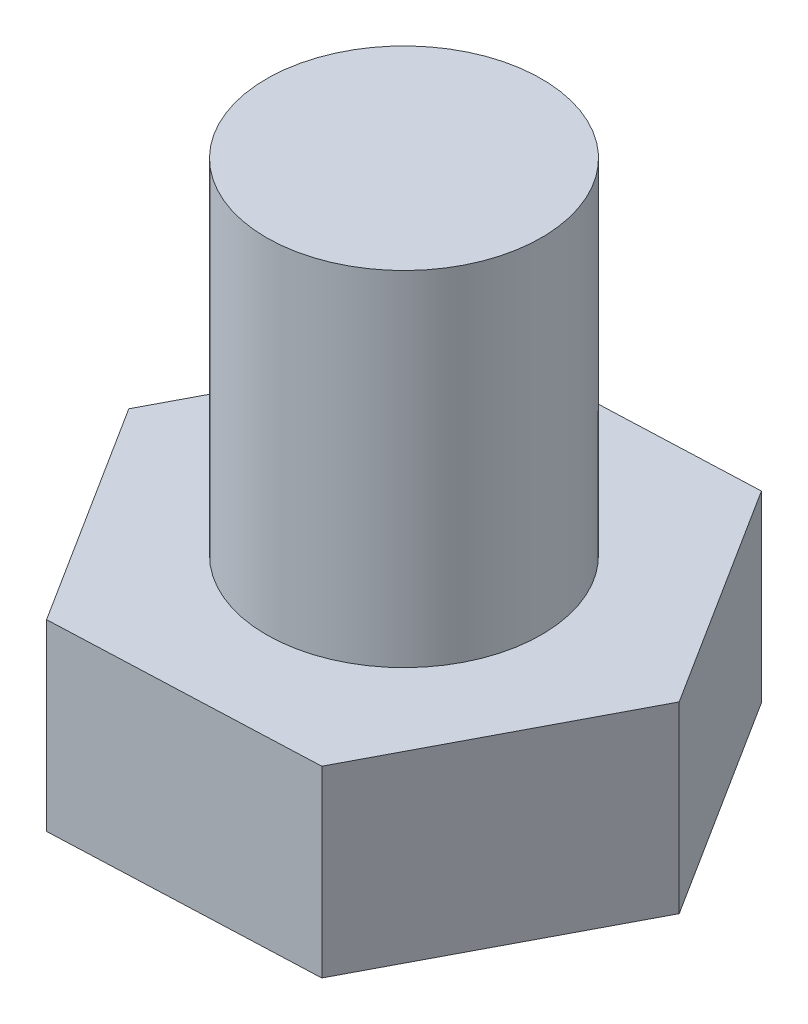
SolidWorks part; units mm, degrees
ref_plane "Front" through (0, 0, 0) normal (0, 0, 1) x (1, 0, 0)
ref_plane "Top" through (0, 0, 0) normal (0, 1, 0) x (1, 0, 0)
ref_plane "Right" through (0, 0, 0) normal (1, 0, 0) x (0, 0, -1)
sketch "Croquis1" plane through (0, 0, 0) normal (0, 1, 0) x (1, 0, 0)
  line L1 (6.1723, -9.7589) -> (11.5376, 0.4659)
  line L2 (11.5376, 0.4659) -> (5.3653, 10.2248)
  line L3 (5.3653, 10.2248) -> (-6.1723, 9.7589)
  line L4 (-6.1723, 9.7589) -> (-11.5376, -0.4659)
  line L5 (-11.5376, -0.4659) -> (-5.3653, -10.2248)
  line L6 (-5.3653, -10.2248) -> (6.1723, -9.7589)
  circle A0 centre (0, 0) radius 10 construction
  dimension "D1" = 20
extrude "Saliente-Extruir1" add sketch "Croquis1" along normal blind 8 contours L3 L4 L5 L6 L1 L2
sketch "Croquis2" plane through (0, 8, 0) normal (0, 1, 0) x (1, 0, 0)
  circle A0 centre (0, 0) radius 6
  dimension "D1" = 12
extrude "Saliente-Extruir2" add sketch "Croquis2" along normal blind 15 contours A0
